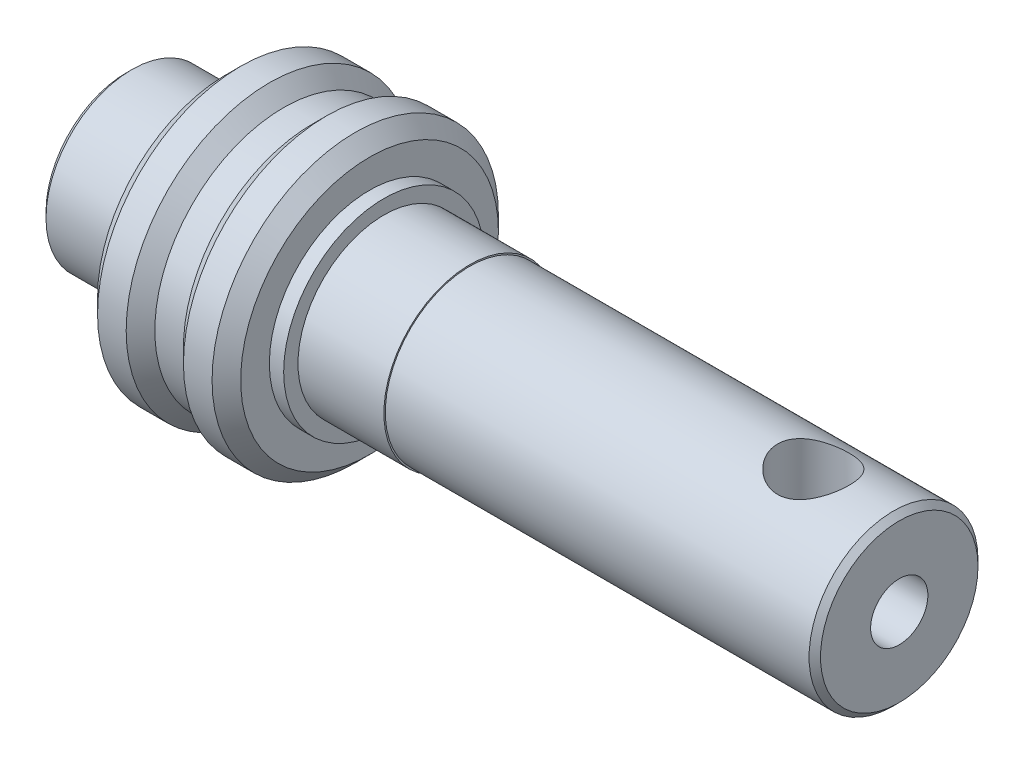
SolidWorks part; units mm, degrees
material "1.4003 (X2CrNi12)"
ref_plane "Ebene vorne" through (0, 0, 0) normal (0, 0, 1) x (1, 0, 0)
ref_plane "Ebene oben" through (0, 0, 0) normal (0, 1, 0) x (1, 0, 0)
ref_plane "Ebene rechts" through (0, 0, 0) normal (1, 0, 0) x (0, 0, -1)
sketch "Skizze1" plane through (0, 0, 0) normal (0, 0, 1) x (1, 0, 0)
  line L0 (0, 0) -> (0, 4) construction
  line L1 (-3, 3) -> (-6, 3)
  line L2 (-3, 3) -> (-3, 3.5)
  line L3 (-3, 3.5) -> (-2.5, 3.5)
  line L4 (-2.5, 3.5) -> (-2.5, 5)
  line L5 (-2.5, 5) -> (-1, 5)
  line L6 (-1, 5) -> (-0.5, 4.5)
  line L7 (-5.5188, 0) -> (-49.9899, 0) construction
  line L8 (-6, 3) -> (-6, 0)
  line L9 (-6, 0) -> (11, 0)
  line L10 (11, 0) -> (11, 1)
  line L11 (1, 5) -> (0.5, 4.5)
  line L12 (2.5, 5) -> (1, 5)
  line L13 (2.5, 3.5) -> (2.5, 5)
  line L14 (3, 3.5) -> (2.5, 3.5)
  line L15 (3, 3) -> (3, 3.5)
  line L16 (3, 3) -> (6, 3)
  line L17 (11, 1) -> (21, 1)
  line L18 (21, 1) -> (21, 2.95)
  line L19 (-0.5, 4.5) -> (0.5, 4.5)
  line L20 (-0.5, 4.5) -> (0, 4) construction
  line L21 (0, 4) -> (0.5, 4.5) construction
  line L22 (6, 3) -> (6, 2.95)
  line L23 (6, 2.95) -> (21, 2.95)
  dimension "D1" = 6
  dimension "D2" = 0.5
  dimension "D3" = 10
  dimension "D4" = 9
  dimension "D5" = 6
  dimension "D6" = 0.5
  dimension "D7" = 3
  dimension "D8" = 2
  dimension "D9" = 10
  dimension "D10" = 18
  dimension "D11" = 2
  dimension "D12" = 5.9
revolve "Rotation1" add sketch "Skizze1" angle 360 about L7
chamfer "Fase1" distance 0.5 angle 45 2 edges at (2.5, 0, -5) (-2.5, 0, -5)
hole_wizard "M3 Gewindebohrung1" positions "3D-Skizze1" profile "Skizze3" tap size "M3" standard "DIN"
sketch3d "3D-Skizze1"
  line L0 (18, 3, 0) -> (21, 3, 0) construction
  line L2 (21, 0, 0) -> (21, 3, 0) construction
  line L3 (11, 0, 0) -> (21, 0, 0) construction
  point P0 (18, 3, 0)
  dimension "D1" = 3
sketch "Skizze3" plane through (18, 3, 0) normal (1, 0, 0) x (0, 0, 1)
  line L0 (0, 0) -> (0, 3.7511)
  line L1 (0, 3.7511) -> (1.25, 3)
  line L2 (1.25, 3) -> (1.25, 0)
  line L5 (1.25, 0) -> (0, 0)
  line L10 (0, 3.7511) -> (-1.25, 3) construction
  line L11 (0, -6.35) -> (0, 107.95) construction
  dimension "Bohrerdurchmesser" = 2.5
  dimension "Bohrungstiefe" = 3
  dimension "Spitzenwinkel" = 118
chamfer "Fase2" distance 0.2 angle 45 2 edges at (21, 0, -2.95) (-6, 0, -3)
